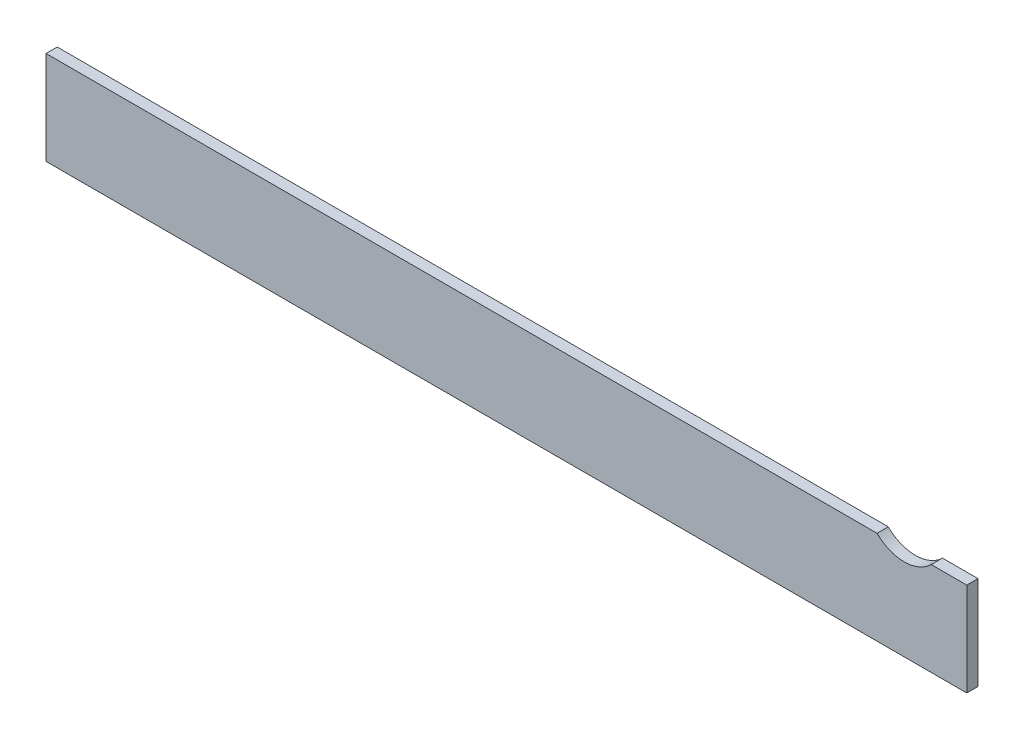
SolidWorks part; units mm, degrees
ref_plane "Alzado" through (0, 0, 0) normal (0, 0, 1) x (1, 0, 0)
ref_plane "Planta" through (0, 0, 0) normal (0, 1, 0) x (1, 0, 0)
ref_plane "Vista lateral" through (0, 0, 0) normal (1, 0, 0) x (0, 0, -1)
sketch "Croquis1" plane through (0, 0, 0) normal (0, 0, 1) x (1, 0, 0)
  line L0 (0, 0) -> (985, 0)
  line L1 (985, 0) -> (985, 100)
  line L2 (985, 100) -> (946.9524, 100)
  line L3 (0, 100) -> (0, 0)
  line L4 (918, 0) -> (918, 129) construction
  line L5 (918, 129) -> (985, 129) construction
  line L6 (985, 129) -> (985, 100) construction
  line L7 (889.0476, 100) -> (0, 100)
  arc A1 (889.0476, 100) -> (946.9524, 100) centre (918, 129) ccw
  dimension "D1" = 985
  dimension "D2" = 100
  dimension "D3" = 129
  dimension "D4" = 67
extrude "Saliente-Extruir1" add sketch "Croquis1" along normal blind 12
